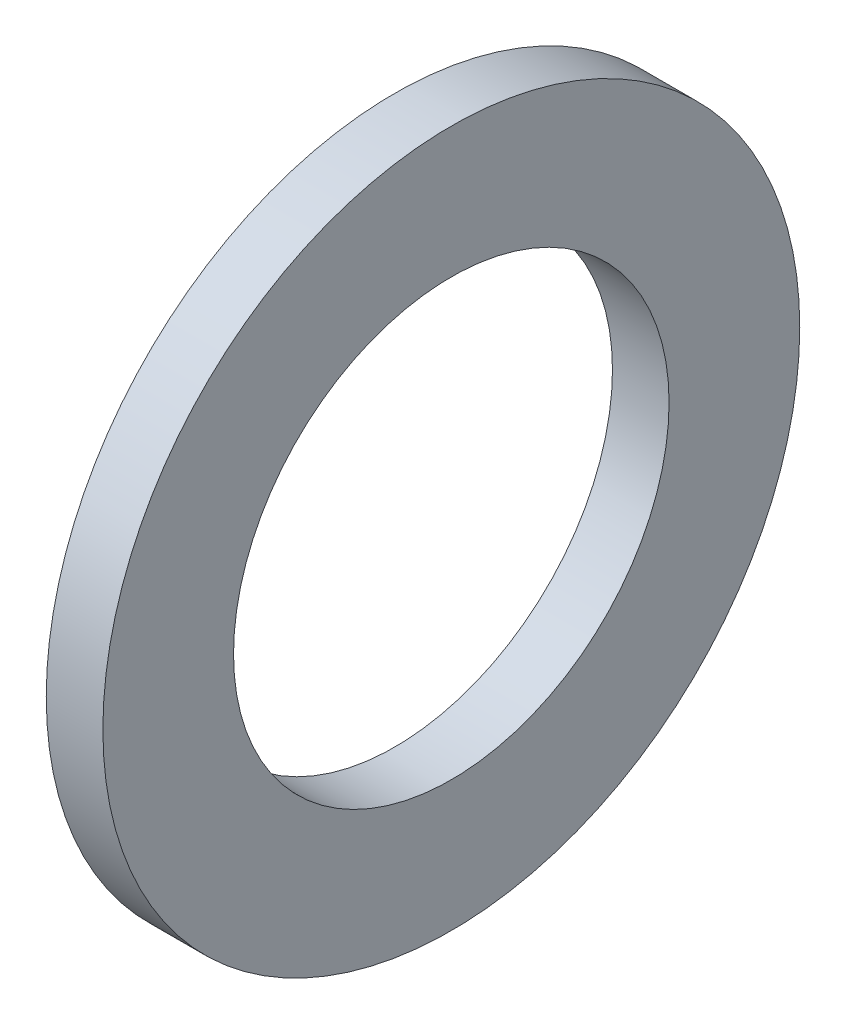
SolidWorks part; units mm, degrees
ref_plane "Front Plane" through (0, 0, 0) normal (0, 0, 1) x (1, 0, 0)
ref_plane "Top Plane" through (0, 0, 0) normal (0, 1, 0) x (1, 0, 0)
ref_plane "Right Plane" through (0, 0, 0) normal (1, 0, 0) x (0, 0, -1)
sketch "Sketch1" plane through (0, 0, 0) normal (1, 0, 0) x (0, 0, -1)
  circle A0 centre (0, 0) radius 6.35
  circle A1 centre (0, 0) radius 10.16
  dimension "D1" = 20.32
  dimension "D2" = 12.7
extrude "Boss-Extrude1" add sketch "Sketch1" along normal blind 1.651
